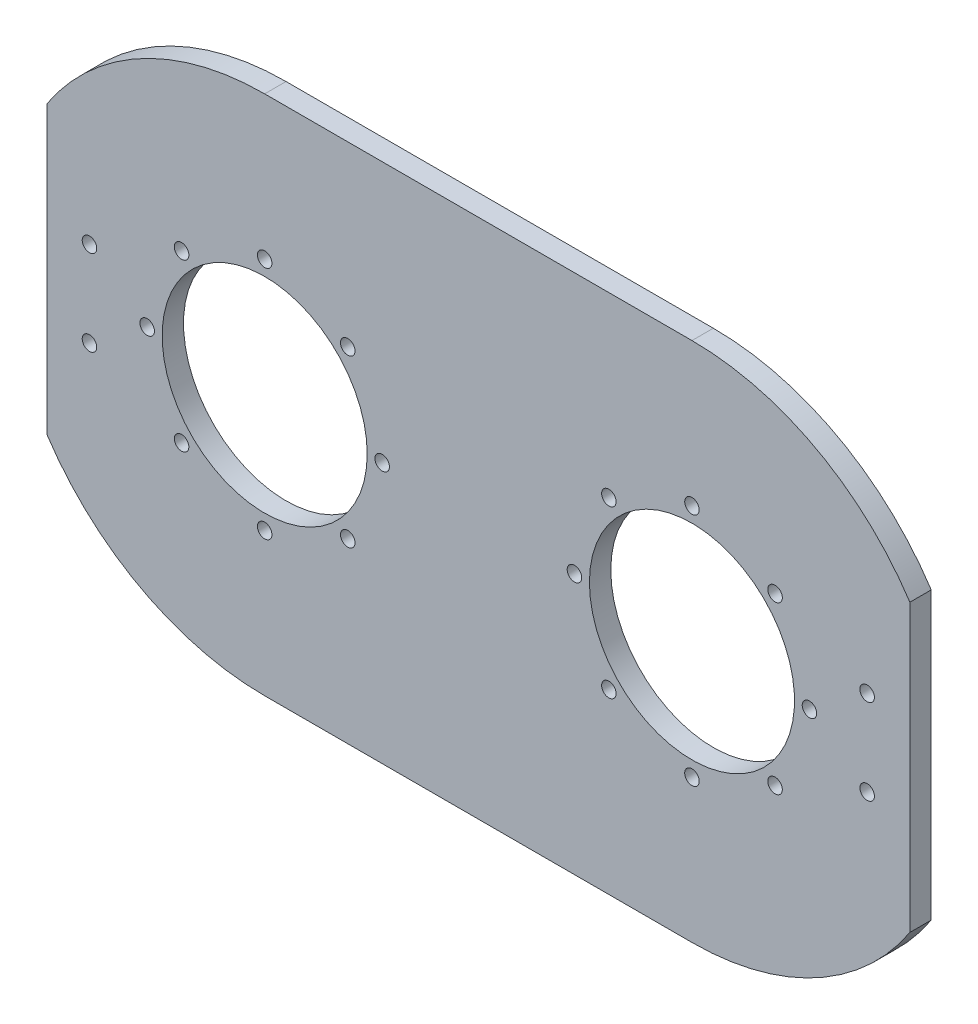
SolidWorks part; units mm, degrees
material "Thornel Mat VMA"
ref_plane "Front" through (0, 0, 0) normal (0, 0, 1) x (1, 0, 0)
ref_plane "Top" through (0, 0, 0) normal (0, 1, 0) x (1, 0, 0)
ref_plane "Right" through (0, 0, 0) normal (1, 0, 0) x (0, 0, -1)
sketch "ｽｹｯﾁ1" plane through (0, 0, 0) normal (0, 0, 1) x (1, 0, 0)
  line L0 (-50, 0) -> (50, 0) construction
  line L1 (-50, 61) -> (50, 61)
  line L2 (-50, -61) -> (50, -61)
  arc A0 (-50, 61) -> (-50, -61) centre (-50, 0) ccw
  arc A1 (50, -61) -> (50, 61) centre (50, 0) ccw
  point P2 (0, 0)
  dimension "D2" = 61
  dimension "D1" = 100
extrude "ﾎﾞｽ - 押し出し1" add sketch "ｽｹｯﾁ1" along normal blind 5
sketch "ｽｹｯﾁ2" plane through (0, 0, 5) normal (0, 0, 1) x (1, 0, 0)
  circle A0 centre (-50, 0) radius 24
  arc A2 (-50, 61) -> (-50, -61) centre (-50, 0) ccw construction
  dimension "D1" = 48
extrude "ｶｯﾄ - 押し出し1" cut sketch "ｽｹｯﾁ2" against normal through all
hole_wizard "M3 すきま穴1" positions "ｽｹｯﾁ3" profile "ｽｹｯﾁ4" hole size "M3" standard "JIS" end condition through all
sketch "ｽｹｯﾁ3" plane through (0, 0, 5) normal (0, 0, 1) x (1, 0, 0)
  circle A0 centre (-50, 0) radius 27.5 construction
  circle A1 centre (-50, 0) radius 24 construction
  point P0 (-50, 27.5)
  point P9 (-50, 27.5)
  dimension "D1" = 55
sketch "ｽｹｯﾁ4" plane through (-50, 27.5, 5) normal (1, 0, 0) x (0, -1, 0)
  line L0 (0, 0) -> (0, 5)
  line L1 (0, 5) -> (1.7, 5)
  line L2 (1.7, 5) -> (1.7, 0)
  line L5 (1.7, 0) -> (0, 0)
  line L11 (0, -6.35) -> (0, 107.95) construction
  dimension "通し穴の直径" = 3.4
  dimension "通し穴の深さ" = 5
pattern_circular "円形ﾊﾟﾀｰﾝ1" count 8 over 360 about axis through (-50, 0, 0) along (0, 0, 1) of "M3 すきま穴1"
mirror "ﾐﾗｰ1" about plane through (0, 0, 0) normal (1, 0, 0) of "ｶｯﾄ - 押し出し1", "円形ﾊﾟﾀｰﾝ1", "M3 すきま穴1"
sketch "ｽｹｯﾁ5" plane through (0, 0, 5) normal (0, 0, 1) x (1, 0, 0)
  line L0 (50, 61) -> (-50, 61) construction
  line L1 (101, -61) -> (-101, -61) construction
  line L2 (101, -61) -> (101, 61) construction
  line L3 (101, 61) -> (-101, 61) construction
  line L4 (-101, -61) -> (-101, 61) construction
  line L5 (101, -61) -> (-101, 61) construction
  line L6 (101, 61) -> (-101, -61) construction
  line L7 (-101, 33.4664) -> (-101, -33.4664)
  arc A0 (-50, 61) -> (-50, -61) centre (-50, 0) ccw construction
  arc A1 (-101, 33.4664) -> (-101, -33.4664) centre (-50, 0) ccw
  circle A2 centre (-50, 0) radius 31 construction
  point P0 (0, 0)
  point P14 (-81, 0)
  dimension "D2" = 62
  dimension "D1" = 20
extrude "ｶｯﾄ - 押し出し2" cut sketch "ｽｹｯﾁ5" against normal through all
hole_wizard "M3 すきま穴2" positions "ｽｹｯﾁ8" profile "ｽｹｯﾁ7" hole size "M3" standard "JIS" end condition through all
sketch "ｽｹｯﾁ8" plane through (0, 0, 5) normal (0, 0, 1) x (1, 0, 0)
  line L0 (-101, 0) -> (0, 0) construction
  line L1 (-101, -33.4664) -> (-101, 33.4664) construction
  line L3 (-91, 45.1664) -> (-91, -45.1664) construction
  arc A0 (-50, 61) -> (-101, 33.4664) centre (-50, 0) ccw construction
  arc A1 (-101, -33.4664) -> (-50, -61) centre (-50, 0) ccw construction
  point P20 (-91, -10)
  point P22 (-91, 10)
  point P29 (-117.463, -11.2103)
  point P30 (0, 0)
  dimension "D1" = 10
  dimension "D2" = 20
sketch "ｽｹｯﾁ7" plane through (-91, 10, 5) normal (1, 0, 0) x (0, -1, 0)
  line L0 (0, 0) -> (0, 5)
  line L1 (0, 5) -> (1.7, 5)
  line L2 (1.7, 5) -> (1.7, 0)
  line L5 (1.7, 0) -> (0, 0)
  line L11 (0, -6.35) -> (0, 107.95) construction
  dimension "通し穴の直径" = 3.4
  dimension "通し穴の深さ" = 5
mirror "ﾐﾗｰ2" about plane through (0, 0, 0) normal (1, 0, 0) of "M3 すきま穴2", "ｶｯﾄ - 押し出し2"
